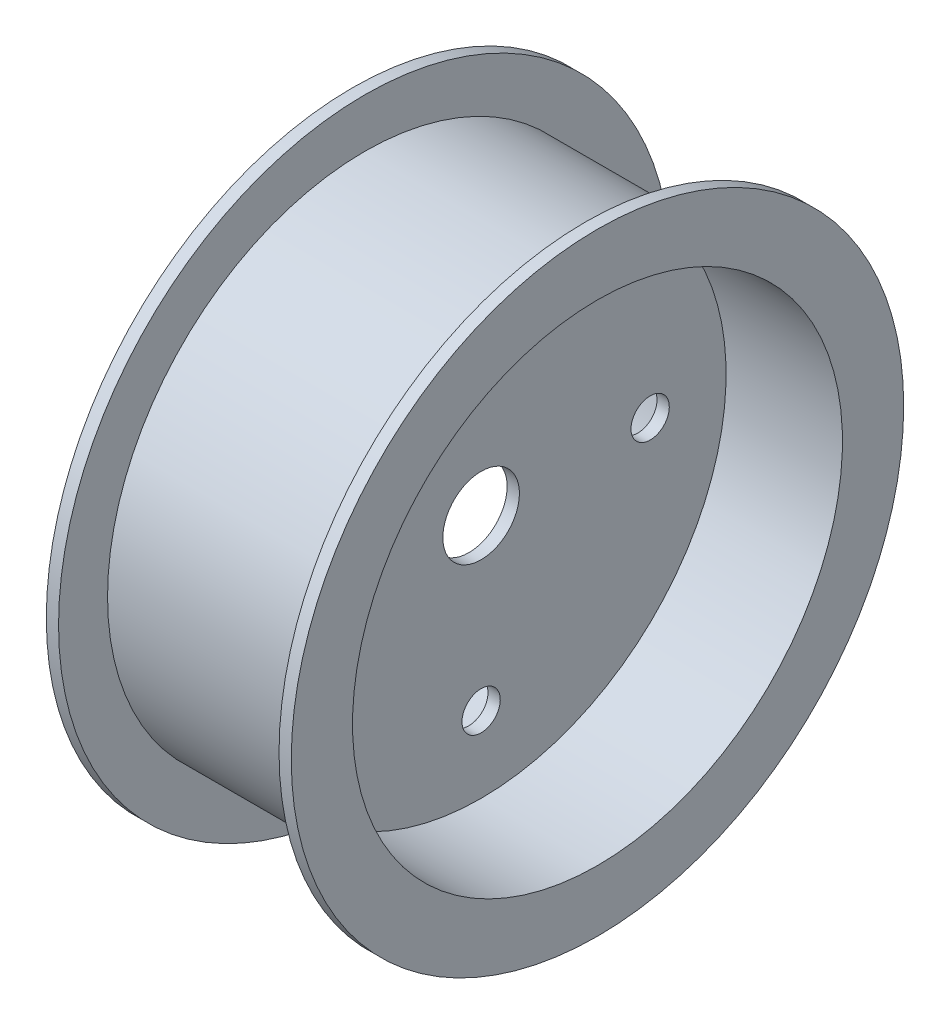
SolidWorks part; units mm, degrees
ref_plane "Front Plane" through (0, 0, 0) normal (0, 0, 1) x (1, 0, 0)
ref_plane "Top Plane" through (0, 0, 0) normal (0, 1, 0) x (1, 0, 0)
ref_plane "Right Plane" through (0, 0, 0) normal (1, 0, 0) x (0, 0, -1)
sketch "Sketch1" plane through (0, 0, 0) normal (0, 0, 1) x (1, 0, 0)
  line L0 (0, 0) -> (0, 53.34) construction
  line L1 (0, 0) -> (-1.27, 0)
  line L2 (0, 0) -> (0, 50.8) construction
  line L3 (0, 50.8) -> (0, 0)
  line L4 (-1.27, 0) -> (-1.27, 50.8)
  line L6 (0, 50.8) -> (0, 53.34)
  line L7 (-1.27, 50.8) -> (-25.4, 50.8)
  line L8 (-25.4, 50.8) -> (-25.4, 63.5)
  line L9 (-22.86, 63.5) -> (-22.86, 53.34)
  line L10 (-22.86, 53.34) -> (0, 53.34)
  line L11 (-25.4, 63.5) -> (-22.86, 63.5)
  dimension "D1" = 2.54
  dimension "D2" = 1.27
  dimension "D5" = 12.7
  dimension "D6" = 24.13
  dimension "D7" = 2.54
revolve "Revolve1" add sketch "Sketch1" angle 360 about L1
mirror "Mirror1" about plane through (0, 0, 0) normal (1, 0, 0) of "Revolve1"
sketch "Sketch2" plane through (1.27, 0, 0) normal (1, 0, 0) x (0, 0, -1)
  line L0 (0, 35.052) -> (0, 0) construction
  line L1 (0, -35.052) -> (0, 0) construction
  line L2 (-35.052, 0) -> (35.052, 0) construction
  circle A0 centre (35.052, 0) radius 3.9688
  circle A1 centre (0, 35.052) radius 3.9688
  circle A2 centre (0, -35.052) radius 3.9688
  circle A3 centre (-35.052, 0) radius 3.9688
  circle A4 centre (0, 0) radius 7.9375
  point P15 (0, 0)
  dimension "D1" = 4
  dimension "D2" = 7.9375
  dimension "D3" = 15.875
extrude "Cut-Extrude1" cut sketch "Sketch2" against normal up to next
